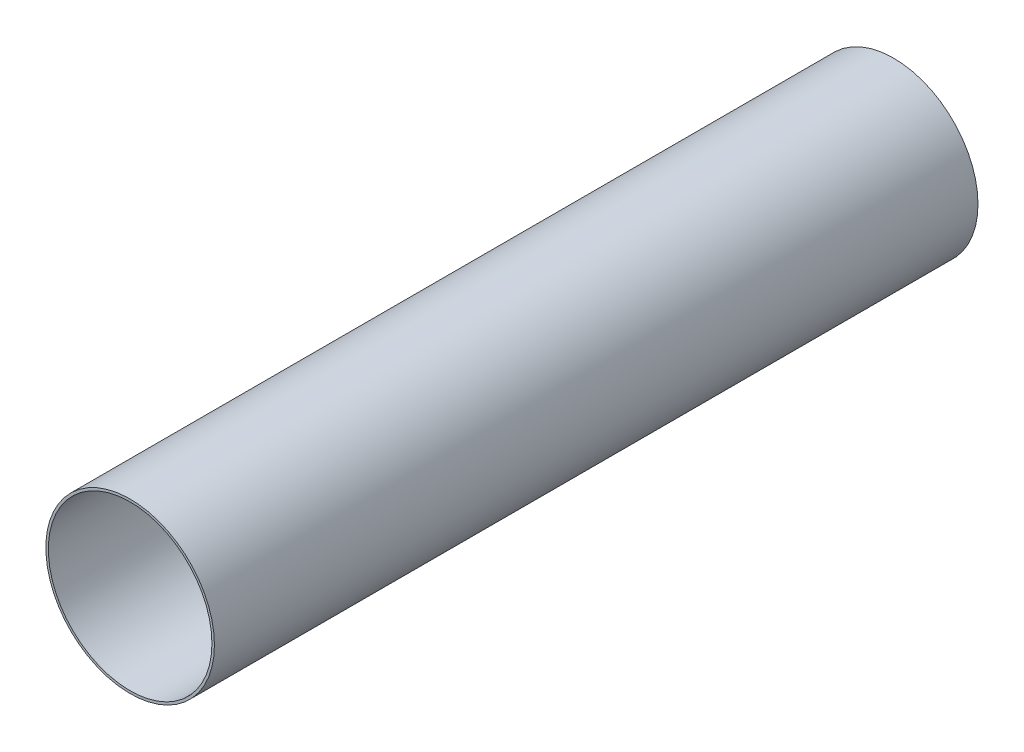
SolidWorks part; units mm, degrees
ref_plane "Front Plane" through (0, 0, 0) normal (0, 0, 1) x (1, 0, 0)
ref_plane "Top Plane" through (0, 0, 0) normal (0, 1, 0) x (1, 0, 0)
ref_plane "Right Plane" through (0, 0, 0) normal (1, 0, 0) x (0, 0, -1)
sketch "Sketch1" plane through (0, 0, 0) normal (0, 0, 1) x (1, 0, 0)
  circle A0 centre (0, 0) radius 39.2557
  circle A1 centre (0, 0) radius 38.1
  dimension "D1" = 76.2
  dimension "D2" = 78.5114
extrude "Boss-Extrude1" add sketch "Sketch1" along normal mid plane 355.6
equation "\"AIRFRAME_OD\"= 5.15in"
equation "\"AIRFRAME_ID\"= 4.99in"
equation "\"FLAT_T\"= 0.125in"
equation "\"NOSE_EXP_L\"= 27in"
equation "\"NOSE_SHOULDER_L\"= 5in"
equation "\"MAIN_L\"= 30in"
equation "\"RECO_COUP_L\"= 10in"
equation "\"RECO_SWITCH_L\"= 2in"
equation "\"DROGUE_L\"= 20in"
equation "\"ATS_FORE_COUP_L\"= 5.5in"
equation "\"ATS_AFT_COUP_L\"= 4.5in"
equation "\"LOWER_L\"= 30in"
equation "\"FIN_N\"= 4"
equation "\"CR_AFT_X\"= 0.5in"
equation "\"CR_FORE_X\"= 9.25in"
equation "\"D1@Sketch1\"=\"MOTOR_ID\""
equation "\"D2@Sketch1\"=\"MOTOR_OD\""
equation "\"D1@Boss-Extrude1\"=\"MOTOR_L\""
equation "\"FIN_ROOT\"= 8in"
equation "\"FIN_X\"= 0.75in"
equation "\"MOTOR_OD\"= 3.091in"
equation "\"MOTOR_ID\"= 3.00in"
equation "\"COUPLER_OD\"= 4.998in"
equation "\"COUPLER_ID\"= 4.85in"
equation "\"RECO_ROD_X\"= 3.5in"
equation "\"ATS_ROD_X\"= 3.75in"
equation "\"MOTOR_L\"= 14in"
equation "\"MOTOR_LOWER_X\"= 2in"
